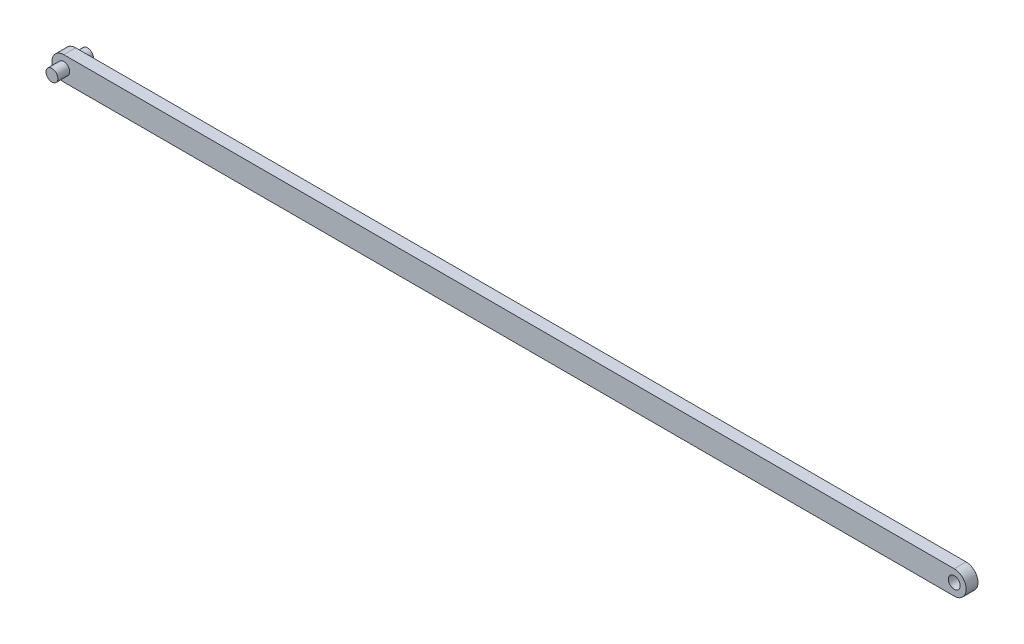
SolidWorks part; units mm, degrees
ref_plane "前视基准面" through (0, 0, 0) normal (0, 0, 1) x (1, 0, 0)
ref_plane "上视基准面" through (0, 0, 0) normal (0, 1, 0) x (1, 0, 0)
ref_plane "右视基准面" through (0, 0, 0) normal (1, 0, 0) x (0, 0, -1)
sketch "草图1" plane through (0, 0, 0) normal (0, 0, 1) x (1, 0, 0)
  line L1 (-50.1592, -2) -> (99.8408, -2)
  line L2 (-50.1592, 2) -> (99.8408, 2)
  arc A0 (99.8408, -2) -> (99.8408, 2) centre (99.8408, 0) ccw
  arc A1 (-50.1592, 2) -> (-50.1592, -2) centre (-50.1592, 0) ccw
  circle A2 centre (99.8408, 0) radius 1
  dimension "D2" = 2
  dimension "D1" = 150
extrude "凸台-拉伸1" add sketch "草图1" along normal blind 2
sketch "草图2" plane through (0, 0, 2) normal (0, 0, 1) x (1, 0, 0)
  circle A0 centre (-50.1592, 0) radius 1
extrude "凸台-拉伸2" add sketch "草图2" along normal blind 2 and the other way blind 4
